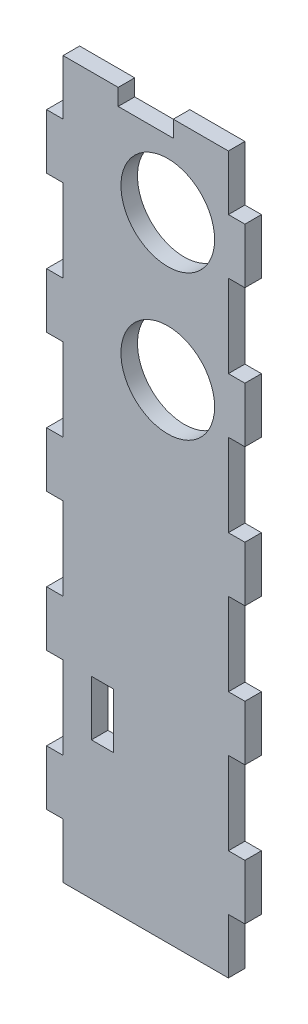
SolidWorks part; units mm, degrees
ref_plane "Plan de face" through (0, 0, 0) normal (0, 0, 1) x (1, 0, 0)
ref_plane "Plan de dessus" through (0, 0, 0) normal (0, 1, 0) x (1, 0, 0)
ref_plane "Plan de droite" through (0, 0, 0) normal (1, 0, 0) x (0, 0, -1)
sketch "Esquisse1" plane through (0, 0, 0) normal (0, 0, 1) x (1, 0, 0)
  line L0 (2.0294, -75.0489) -> (-27.9706, -75.0489)
  line L2 (-27.9706, -15.0489) -> (-30.9706, -15.0489)
  line L3 (-30.9706, -15.0489) -> (-30.9706, -5.0489)
  line L4 (-30.9706, -5.0489) -> (-27.9706, -5.0489)
  line L5 (-27.9706, -5.0489) -> (-27.9706, 9.9511)
  line L6 (-27.9706, 9.9511) -> (-30.9706, 9.9511)
  line L7 (-30.9706, 9.9511) -> (-30.9706, 19.9511)
  line L8 (-30.9706, 19.9511) -> (-27.9706, 19.9511)
  line L9 (-27.9706, 19.9511) -> (-27.9706, 34.9511)
  line L10 (-27.9706, 34.9511) -> (-30.9706, 34.9511)
  line L11 (-30.9706, 34.9511) -> (-30.9706, 44.9511)
  line L12 (-30.9706, 44.9511) -> (-27.9706, 44.9511)
  line L13 (-27.9706, 44.9511) -> (-27.9706, 54.9511)
  line L14 (-27.9706, 54.9511) -> (-17.9706, 54.9511)
  line L15 (2.0294, 54.9511) -> (2.0294, 44.9511)
  line L16 (2.0294, 44.9511) -> (5.0294, 44.9511)
  line L17 (5.0294, 44.9511) -> (5.0294, 34.9511)
  line L18 (5.0294, 34.9511) -> (2.0294, 34.9511)
  line L19 (2.0294, 34.9511) -> (2.0294, 19.9511)
  line L20 (2.0294, 19.9511) -> (5.0294, 19.9511)
  line L21 (5.0294, 19.9511) -> (5.0294, 9.9511)
  line L22 (5.0294, 9.9511) -> (2.0294, 9.9511)
  line L23 (2.0294, 9.9511) -> (2.0294, -5.0489)
  line L24 (2.0294, -5.0489) -> (5.0294, -5.0489)
  line L25 (5.0294, -5.0489) -> (5.0294, -15.0489)
  line L26 (5.0294, -15.0489) -> (2.0294, -15.0489)
  line L28 (-27.9706, -15.0489) -> (-27.9706, -30.0489)
  line L29 (-27.9706, -30.0489) -> (-30.9706, -30.0489)
  line L30 (-30.9706, -30.0489) -> (-30.9706, -40.0489)
  line L31 (-30.9706, -40.0489) -> (-27.9706, -40.0489)
  line L32 (-27.9706, -40.0489) -> (-27.9706, -55.0489)
  line L33 (-27.9706, -55.0489) -> (-30.9706, -55.0489)
  line L34 (-30.9706, -55.0489) -> (-30.9706, -65.0489)
  line L35 (-30.9706, -65.0489) -> (-27.9706, -65.0489)
  line L36 (-27.9706, -65.0489) -> (-27.9706, -75.0489)
  line L37 (-12.9706, 54.9511) -> (-12.9706, -95.9492) construction
  line L38 (2.0294, -15.0489) -> (2.0294, -30.0489)
  line L39 (2.0294, -30.0489) -> (5.0294, -30.0489)
  line L40 (5.0294, -30.0489) -> (5.0294, -40.0489)
  line L41 (5.0294, -40.0489) -> (2.0294, -40.0489)
  line L42 (2.0294, -40.0489) -> (2.0294, -55.0489)
  line L43 (2.0294, -55.0489) -> (5.0294, -55.0489)
  line L44 (5.0294, -55.0489) -> (5.0294, -65.0489)
  line L45 (5.0294, -65.0489) -> (2.0294, -65.0489)
  line L46 (2.0294, -65.0489) -> (2.0294, -75.0489)
  line L47 (-7.9706, 54.9511) -> (-7.9706, 51.9511)
  line L48 (-18.8343, -40.0489) -> (-22.8343, -40.0489)
  line L49 (-18.8343, -40.0489) -> (-18.8343, -50.0489)
  line L50 (-18.8343, -50.0489) -> (-22.8343, -50.0489)
  line L51 (-22.8343, -40.0489) -> (-22.8343, -50.0489)
  line L52 (-7.9706, 51.9511) -> (-17.9706, 51.9511)
  line L53 (-17.9706, 51.9511) -> (-17.9706, 54.9511)
  line L54 (-7.9706, 54.9511) -> (2.0294, 54.9511)
  circle A0 centre (-8.9706, 39.768) radius 8.5
  circle A1 centre (-8.9706, 13.468) radius 8.5
  point P26 (-27.9706, 49.9511)
  point P59 (-20.8343, -50.0489)
  dimension "D30" = 17
  dimension "D31" = 17
  dimension "D1" = 130
  dimension "D2" = 3
  dimension "D3" = 10
  dimension "D4" = 10
  dimension "D5" = 15
  dimension "D6" = 10
  dimension "D7" = 3
  dimension "D8" = 15
  dimension "D9" = 10
  dimension "D10" = 3
  dimension "D11" = 30
  dimension "D12" = 15
  dimension "D13" = 10
  dimension "D14" = 3
  dimension "D15" = 15
  dimension "D16" = 10
  dimension "D17" = 3
  dimension "D18" = 15
  dimension "D19" = 10
  dimension "D20" = 3
  dimension "D21" = 15
  dimension "D22" = 10
  dimension "D23" = 3
  dimension "D24" = 10
  dimension "D25" = 10
  dimension "D26" = 4
  dimension "D27" = 10
  dimension "D28" = 10
  dimension "D29" = 3
  dimension "D32" = 26.3
  dimension "D33" = 25
  dimension "D35" = 11
extrude "Boss.-Extru.1" add sketch "Esquisse1" along normal blind 3
